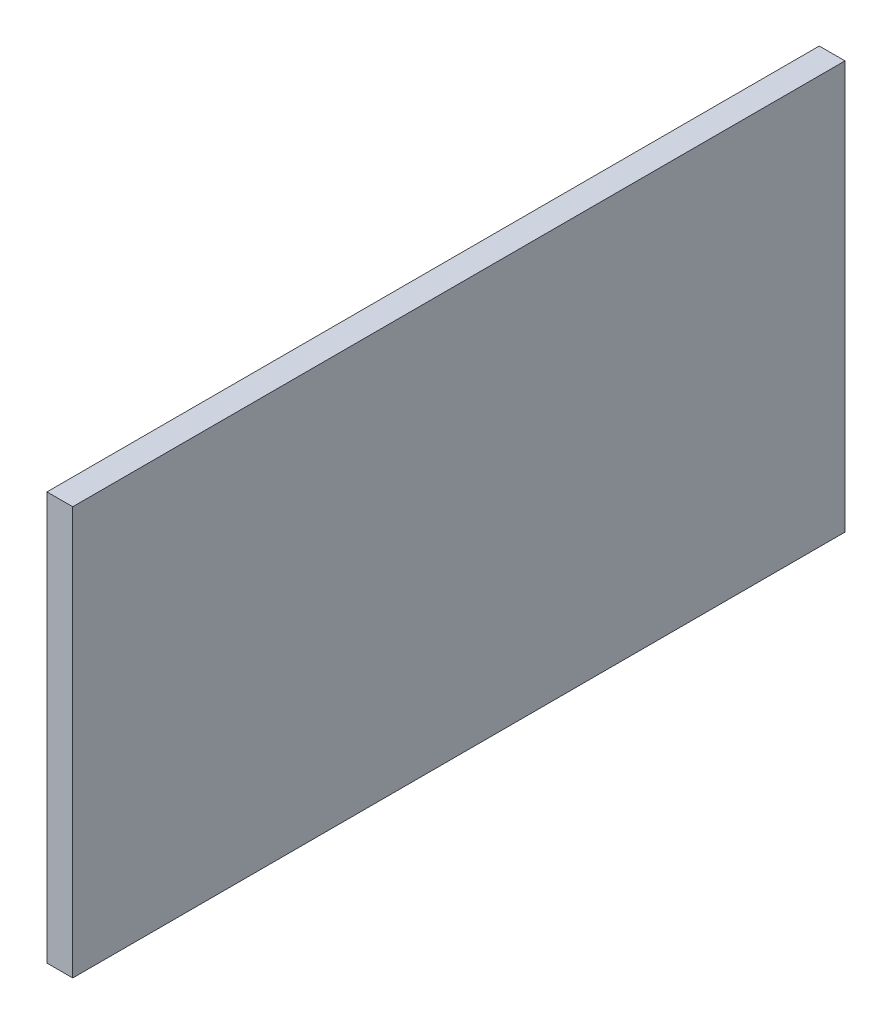
SolidWorks part; units mm, degrees
ref_plane "Front Plane" through (0, 0, 0) normal (0, 0, 1) x (1, 0, 0)
ref_plane "Top Plane" through (0, 0, 0) normal (0, 1, 0) x (1, 0, 0)
ref_plane "Right Plane" through (0, 0, 0) normal (1, 0, 0) x (0, 0, -1)
sketch "Sketch1" plane through (0, 0, 0) normal (1, 0, 0) x (0, 0, -1)
  line L1 (-187.5, 99.085) -> (187.5, 99.085)
  line L2 (-187.5, 99.085) -> (-187.5, -99.085)
  line L3 (-187.5, -99.085) -> (187.5, -99.085)
  line L4 (187.5, 99.085) -> (187.5, -99.085)
  line L5 (-187.5, 99.085) -> (187.5, -99.085) construction
  line L6 (-187.5, -99.085) -> (187.5, 99.085) construction
  point P0 (0, 0)
  dimension "D1" = 375
  dimension "D2" = 198.17
extrude "Boss-Extrude1" add sketch "Sketch1" along normal blind 12.5
